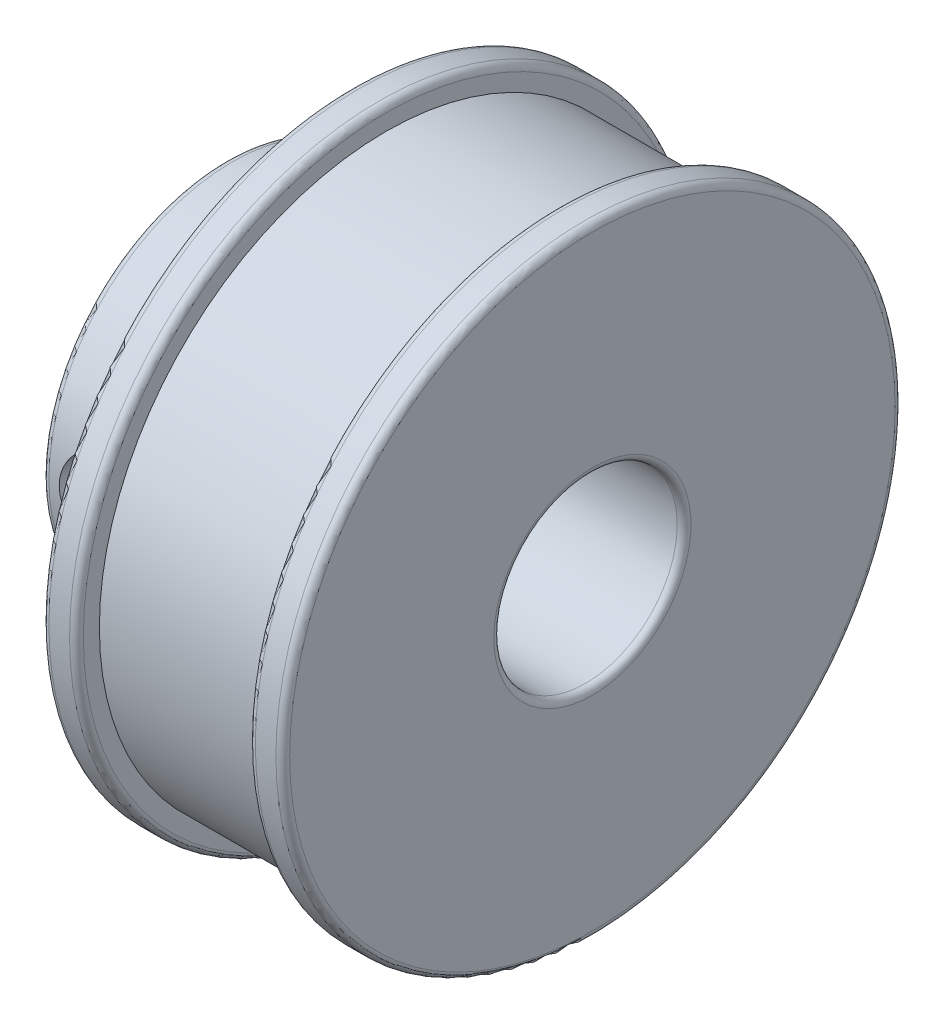
SolidWorks part; units mm, degrees
ref_plane "Front Plane" through (0, 0, 0) normal (0, 0, 1) x (1, 0, 0)
ref_plane "Top Plane" through (0, 0, 0) normal (0, 1, 0) x (1, 0, 0)
ref_plane "Right Plane" through (0, 0, 0) normal (1, 0, 0) x (0, 0, -1)
sketch "Sketch1" plane through (0, 0, 0) normal (0, 1, 0) x (1, 0, 0)
  line L0 (0, 0) -> (0, 4) construction
  line L1 (0, 4) -> (0, 8)
  line L2 (0, 8) -> (5.5, 8)
  line L4 (7, 12.5) -> (14.5, 12.5)
  line L5 (14.5, 12.5) -> (14.5, 13.5)
  line L6 (14.5, 13.5) -> (16, 13.5)
  line L7 (16, 13.5) -> (16, 4)
  line L8 (16, 4) -> (0, 4)
  line L9 (0, 0) -> (19.664, 0) construction
  line L10 (7, 13.5) -> (7, 12.5)
  line L11 (7, 13.5) -> (5.5, 13.5)
  line L12 (5.5, 13.5) -> (5.5, 8)
  dimension "D1" = 16
  dimension "2.5" = 4
  dimension "D2" = 8
  dimension "D3" = 1.5
  dimension "D4" = 7.5
  dimension "D5" = 1.5
  dimension "D6" = 13.5
  dimension "D7" = 12.5
revolve "Revolve1" add sketch "Sketch1" angle 360 about L9
fillet "Fillet1" radius 0.3 7 edges at (0, 0, 8) (16, 0, 13.5) (14.5, 0, 13.5) (0, 0, 4) (16, 0, 4) (7, 0, 13.5) (5.5, 0, 13.5)
sketch "Sketch2" plane through (0, 0, 0) normal (0, 0, 1) x (1, 0, 0)
  line L0 (0, 0) -> (5.5, 0) construction
  line L2 (5.5, 8) -> (5.5, -8) construction
  circle A0 centre (2.75, 0) radius 2
  point P3 (0, 0)
  dimension "D1" = 4
extrude "Cut-Extrude1" cut sketch "Sketch2" against normal through all both and the other way through all
